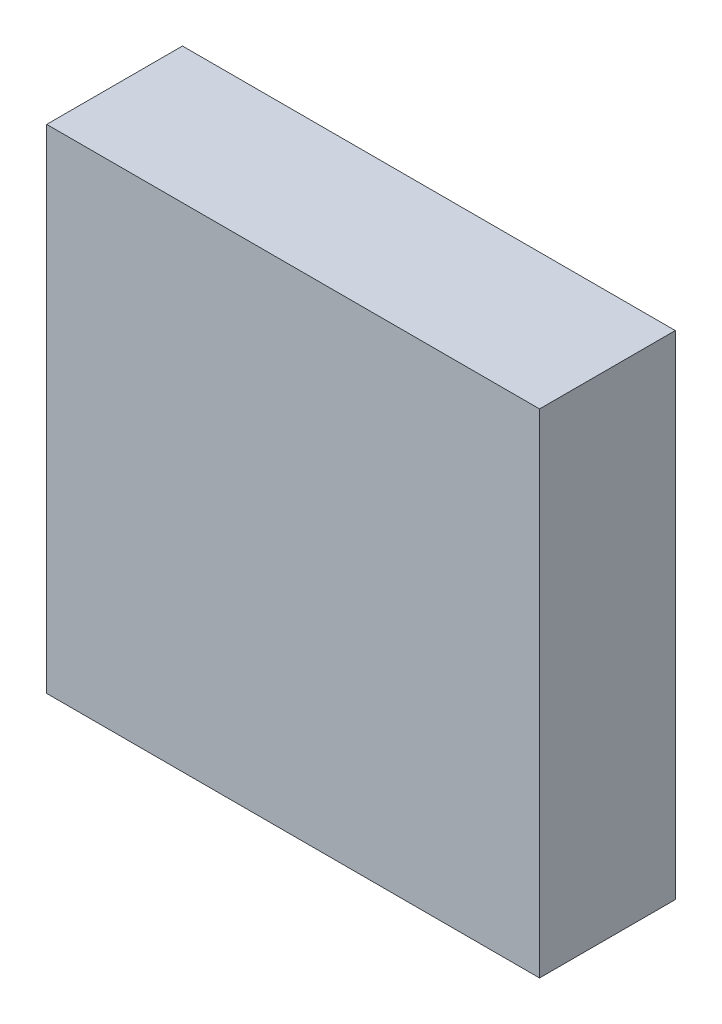
SolidWorks part; units mm, degrees
ref_plane "Спереди" through (0, 0, 0) normal (0, 0, 1) x (1, 0, 0)
ref_plane "Сверху" through (0, 0, 0) normal (0, 1, 0) x (1, 0, 0)
ref_plane "Справа" through (0, 0, 0) normal (1, 0, 0) x (0, 0, -1)
sketch "Эскиз1" plane through (0, 0, 0) normal (0, 0, 1) x (1, 0, 0)
  line L0 (0, 0) -> (77.5, 0)
  line L1 (0, 0) -> (0, 77.5)
  line L2 (77.5, 0) -> (77.5, 77.5)
  line L3 (0, 77.5) -> (77.5, 77.5)
  line L4 (-3, 80.5) -> (80.5, 80.5)
  line L5 (-3, 80.5) -> (-3, -3)
  line L6 (80.5, 80.5) -> (80.5, -3)
  line L7 (-3, -3) -> (80.5, -3)
  dimension "D1" = 77.5
  dimension "D2" = 77.5
  dimension "D3" = 3
  dimension "D4" = 3
  dimension "D5" = 3
  dimension "D6" = 3
extrude "Бобышка-Вытянуть1" add sketch "Эскиз1" along normal blind 20
chamfer "Фаска1" distance 1.5 angle 45 4 edges at (38.75, 77.5, 0) (0, 38.75, 0) (38.75, 0, 0) (77.5, 38.75, 0)
sketch "Эскиз2" plane through (0, 0, 20) normal (0, 0, 1) x (1, 0, 0)
  line L0 (-3, 80.5) -> (-3, -3) construction
  line L1 (80.5, 80.5) -> (-3, 80.5) construction
  line L2 (-3, -3) -> (80.5, -3) construction
  line L3 (80.5, -3) -> (80.5, 80.5) construction
  line L4 (-3, 80.5) -> (-3, -3)
  line L5 (80.5, 80.5) -> (-3, 80.5)
  line L6 (-3, -3) -> (80.5, -3)
  line L7 (80.5, -3) -> (80.5, 80.5)
extrude "Бобышка-Вытянуть2" add sketch "Эскиз2" along normal blind 3
sketch "Эскиз3" plane through (0, 0, 23) normal (0, 0, 1) x (1, 0, 0)
  line L0 (38.75, -3) -> (38.75, 80.5) construction
  line L1 (-3, -3) -> (80.5, -3) construction
  line L2 (80.5, 80.5) -> (-3, 80.5) construction
  line L3 (-3, 38.75) -> (80.5, 38.75) construction
  line L4 (-3, 80.5) -> (-3, -3) construction
  line L5 (80.5, -3) -> (80.5, 80.5) construction
ref_plane "Плоскость1" through (0, 38.75, 0) normal (0, -1, 0) x (1, 0, 0)
ref_plane "Плоскость2" through (38.75, 0, 0) normal (1, 0, 0) x (0, 1, 0)
